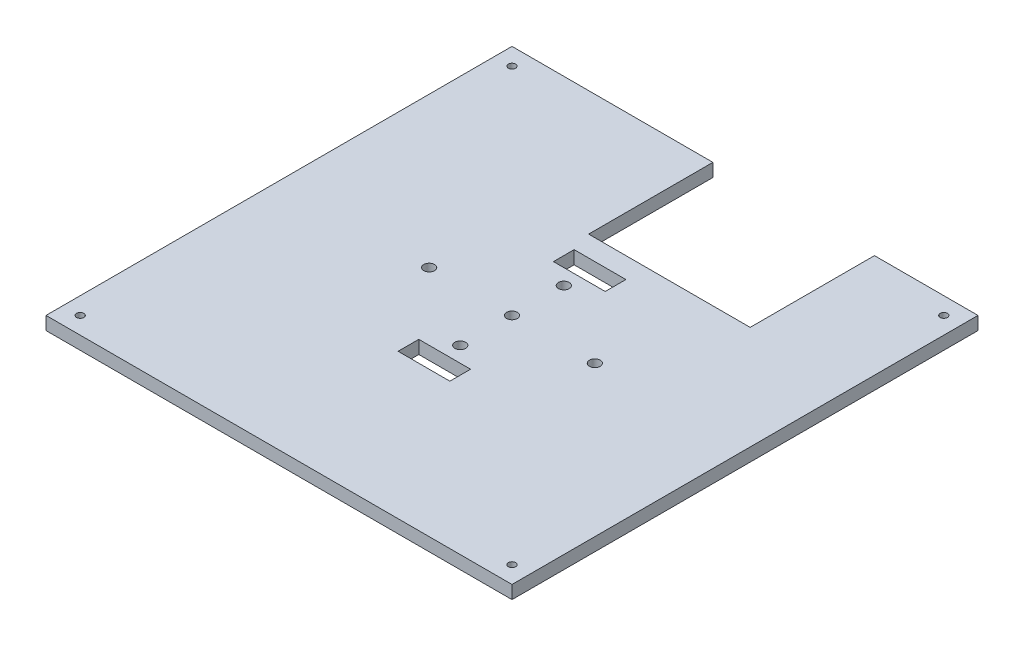
SolidWorks part; units mm, degrees
ref_plane "Front Plane" through (0, 0, 0) normal (0, 0, 1) x (1, 0, 0)
ref_plane "Top Plane" through (0, 0, 0) normal (0, 1, 0) x (1, 0, 0)
ref_plane "Right Plane" through (0, 0, 0) normal (1, 0, 0) x (0, 0, -1)
sketch "Sketch1" plane through (0, 0, 0) normal (0, 1, 0) x (1, 0, 0)
  line L1 (0, 0) -> (225, 0)
  line L2 (0, 0) -> (0, 225)
  line L3 (0, 225) -> (225, 225)
  line L4 (225, 0) -> (225, 225)
  line L5 (0, 0) -> (225, 225) construction
  line L6 (0, 225) -> (225, 0) construction
  point P4 (112.5, 112.5)
  dimension "D1" = 225
  dimension "D2" = 225
extrude "Boss-Extrude1" add sketch "Sketch1" along normal blind 6.35
sketch "Sketch2" plane through (0, 6.35, 0) normal (0, 1, 0) x (1, 0, 0)
  line L0 (222.5, 222.5) -> (222.5, 225) construction
  line L1 (2.5, 2.5) -> (222.5, 2.5) construction
  line L2 (2.5, 2.5) -> (2.5, 222.5) construction
  line L3 (2.5, 222.5) -> (222.5, 222.5) construction
  line L4 (222.5, 2.5) -> (222.5, 222.5) construction
  line L5 (112.5, 222.5) -> (112.5, 2.5) construction
  line L6 (2.5, 112.5) -> (222.5, 112.5) construction
  line L7 (225, 225) -> (0, 225) construction
  line L8 (222.5, 222.5) -> (225, 222.5) construction
  line L9 (225, 0) -> (225, 225) construction
  line L10 (2.5, 2.5) -> (0, 2.5) construction
  line L11 (0, 225) -> (0, 0) construction
  line L12 (2.5, 2.5) -> (2.5, 0) construction
  line L13 (0, 0) -> (225, 0) construction
  circle A0 centre (216.74, 216.74) radius 1.75
  circle A1 centre (8.26, 216.74) radius 1.75
  circle A2 centre (216.74, 8.26) radius 1.75
  circle A3 centre (8.26, 8.26) radius 1.75
  dimension "D2" = 5.76
  dimension "D4" = 3.5
  dimension "D1" = 220
  dimension "D3" = 5.76
extrude "Cut-Extrude1" cut sketch "Sketch2" against normal through all
sketch "Sketch3" plane through (0, 6.35, 0) normal (0, 1, 0) x (1, 0, 0)
  line L0 (112.5, 0) -> (112.5, 225) construction
  line L1 (0, 0) -> (225, 0) construction
  line L2 (225, 225) -> (0, 225) construction
  line L3 (225, 112.5) -> (0, 112.5) construction
  line L4 (225, 0) -> (225, 225) construction
  line L5 (0, 225) -> (0, 0) construction
  line L6 (125, 70) -> (100, 70)
  line L7 (175, 225) -> (97, 225)
  line L8 (175, 225) -> (175, 165)
  line L9 (175, 165) -> (97, 165)
  line L10 (97, 225) -> (97, 165)
  line L11 (125, 145) -> (100, 145)
  line L12 (125, 145) -> (125, 155)
  line L13 (125, 155) -> (100, 155)
  line L14 (100, 145) -> (100, 155)
  line L15 (100, 80) -> (100, 70)
  line L16 (125, 80) -> (100, 80)
  line L17 (125, 80) -> (125, 70)
  circle A0 centre (152.5, 112.5) radius 2.6
  circle A1 centre (112.5, 112.5) radius 2.6
  circle A2 centre (72.5, 112.5) radius 2.6
  circle A3 centre (112.5, 87.5) radius 2.6
  circle A4 centre (112.5, 137.5) radius 2.6
  point P30 (100, 150)
  point P31 (112.5, 145)
  dimension "D5" = 5.2
  dimension "D1" = 25
  dimension "D2" = 25
  dimension "D3" = 40
  dimension "D4" = 40
  dimension "D6" = 52.5
  dimension "D7" = 50
  dimension "D8" = 97
  dimension "D9" = 37.5
  dimension "D10" = 10
  dimension "D11" = 25
extrude "Cut-Extrude2" cut sketch "Sketch3" against normal up to surface (6.35 mm away) up to face at (8.26, 0, -218.49)
